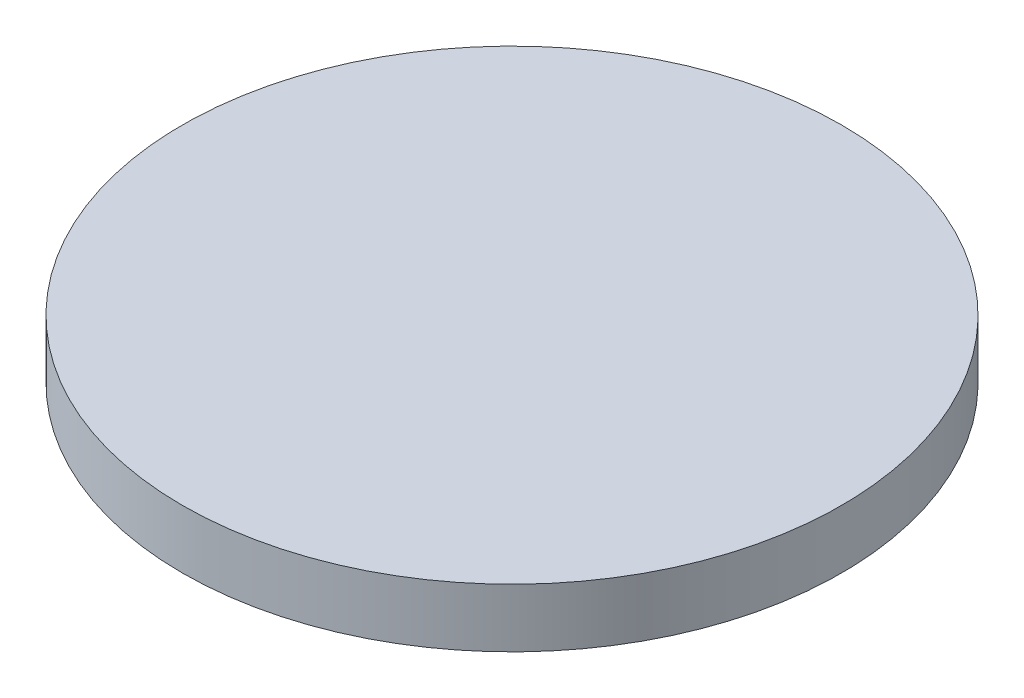
SolidWorks part; units mm, degrees
ref_plane "Alzado" through (0, 0, 0) normal (0, 0, 1) x (1, 0, 0)
ref_plane "Planta" through (0, 0, 0) normal (0, 1, 0) x (1, 0, 0)
ref_plane "Vista lateral" through (0, 0, 0) normal (1, 0, 0) x (0, 0, -1)
sketch "Croquis1" plane through (0, 0, 0) normal (0, 1, 0) x (1, 0, 0)
  circle A0 centre (0, 0) radius 22.5
  dimension "D1" = 45
extrude "Saliente-Extruir1" add sketch "Croquis1" along normal blind 4
